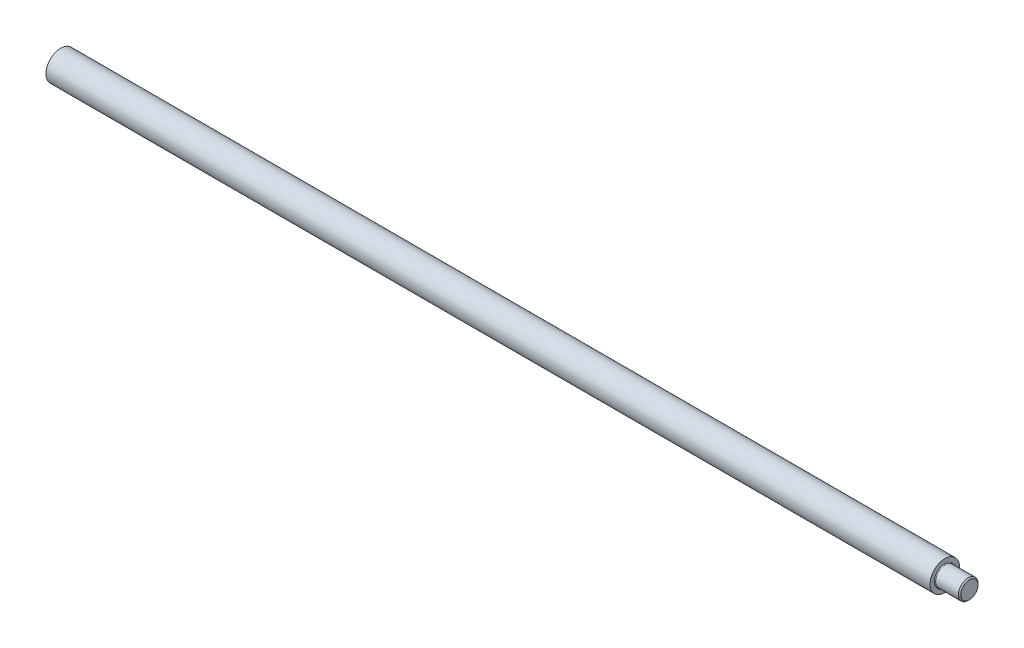
SolidWorks part; units mm, degrees
ref_plane "Piano frontale" through (0, 0, 0) normal (0, 0, 1) x (1, 0, 0)
ref_plane "Piano superiore" through (0, 0, 0) normal (0, 1, 0) x (1, 0, 0)
ref_plane "Piano destro" through (0, 0, 0) normal (1, 0, 0) x (0, 0, -1)
sketch "Sketch1" plane through (0, 0, 0) normal (0, 0, 1) x (1, 0, 0)
  line L0 (10, 5.6842) -> (10, 0)
  line L1 (10, 0) -> (360, 0)
  line L2 (360, 0) -> (360, 3.3158)
  line L3 (360, 3.3158) -> (359.5263, 3.7895)
  line L4 (359.5263, 3.7895) -> (350.8105, 3.7895)
  line L5 (350.5263, 4.0737) -> (350.5263, 5.6842)
  line L6 (350.5263, 5.6842) -> (10, 5.6842)
  line L7 (10, 0) -> (360, 0) construction
  arc A0 (350.8105, 3.7895) -> (350.5263, 4.0737) centre (350.8105, 4.0737) cw
  dimension "D1" = 350
revolve "Revolve1" add sketch "Sketch1" angle 360 about L7
